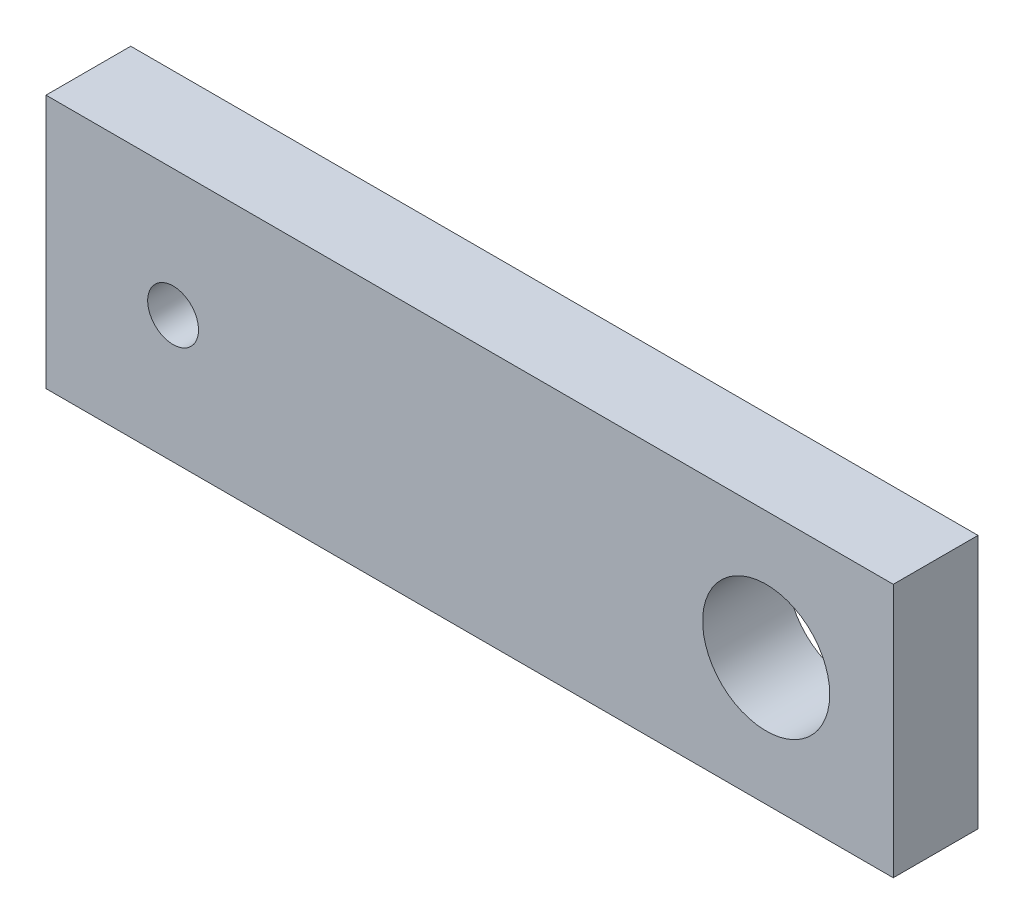
SolidWorks part; units mm, degrees
ref_plane "Front Plane" through (0, 0, 0) normal (0, 0, 1) x (1, 0, 0)
ref_plane "Top Plane" through (0, 0, 0) normal (0, 1, 0) x (1, 0, 0)
ref_plane "Right Plane" through (0, 0, 0) normal (1, 0, 0) x (0, 0, -1)
sketch "Sketch1" plane through (0, 0, 0) normal (0, 0, 1) x (1, 0, 0)
  line L1 (0, 0) -> (-20, 0)
  line L2 (0, 0) -> (0, 6)
  line L3 (0, 6) -> (-20, 6)
  line L4 (-20, 0) -> (-20, 6)
  circle A0 centre (-17, 3) radius 0.6
  circle A1 centre (-3, 3) radius 1.5
  dimension "D3" = 1.2
  dimension "D4" = 3
  dimension "D5" = 3
  dimension "D6" = 3
  dimension "D7" = 3
  dimension "D8" = 3
  dimension "D1" = 6
  dimension "D2" = 20
extrude "Boss-Extrude1" add sketch "Sketch1" along normal blind 2
